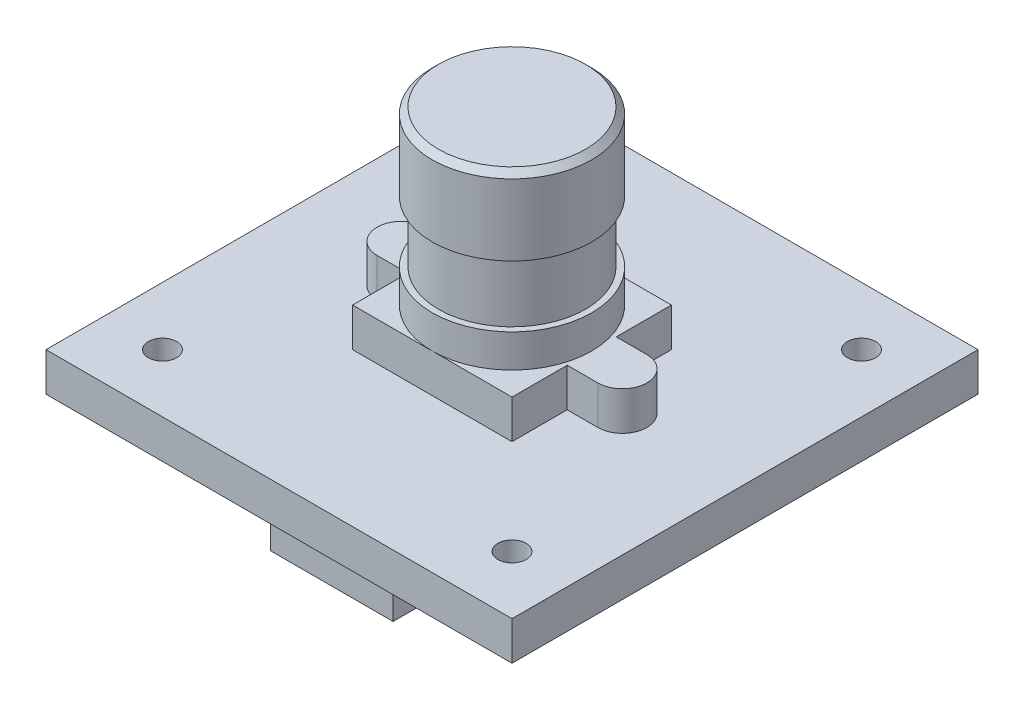
SolidWorks part; units mm, degrees
ref_plane "前视基准面" through (0, 0, 0) normal (0, 0, 1) x (1, 0, 0)
ref_plane "上视基准面" through (0, 0, 0) normal (0, 1, 0) x (1, 0, 0)
ref_plane "右视基准面" through (0, 0, 0) normal (1, 0, 0) x (0, 0, -1)
sketch "草图2" plane through (0, 0, 0) normal (0, 1, 0) x (1, 0, 0)
  line L0 (0, -55) -> (0, 55) construction
  line L1 (-19, 19) -> (19, 19)
  line L2 (-19, 19) -> (-19, -19)
  line L3 (-19, -19) -> (19, -19)
  line L4 (19, 19) -> (19, -19)
  line L5 (-55, 0) -> (55, 0) construction
  circle A0 centre (14.25, 14.25) radius 1.15
  circle A1 centre (-14.25, 14.25) radius 1.15
  circle A2 centre (14.25, -14.25) radius 1.15
  circle A3 centre (-14.25, -14.25) radius 1.15
  dimension "D5" = 2.3
  dimension "D1" = 38
  dimension "D2" = 38
  dimension "D3" = 19
  dimension "D4" = 19
  dimension "D6" = 4.75
  dimension "D7" = 4.75
extrude "凸台-拉伸1" add sketch "草图2" along normal blind 3.15
sketch "草图3" plane through (0, 0, 0) normal (0, 1, 0) x (1, 0, 0)
  line L0 (9, 2) -> (6.5, 2)
  line L1 (-6.5, 6.5) -> (6.5, 6.5)
  line L2 (-6.5, 6.5) -> (-6.5, -6.5)
  line L3 (-6.5, -6.5) -> (6.5, -6.5)
  line L4 (6.5, 6.5) -> (6.5, -6.5)
  line L5 (9, -2) -> (6.5, -2)
  line L6 (0, -1.65) -> (0, 1.65) construction
  line L7 (-9, -2) -> (-6.5, -2)
  line L8 (-9, 2) -> (-6.5, 2)
  arc A0 (9, -2) -> (9, 2) centre (9, 0) ccw
  arc A1 (-9, -2) -> (-9, 2) centre (-9, 0) cw
  dimension "D5" = 4
  dimension "D1" = 13
  dimension "D2" = 13
  dimension "D3" = 6.5
  dimension "D4" = 6.5
  dimension "D6" = 2.5
extrude "凸台-拉伸2" add sketch "草图3" along normal blind 3.15 from surface at 3.15 contours A1 L7 L2 L8 | L4 L1 L2 L3 | L5 A0 L0 L4 starting at face at (14.25, 3.15, 13.1)
sketch "草图4" plane through (0, 0, 0) normal (0, 1, 0) x (1, 0, 0)
  circle A0 centre (0, 0) radius 6.5
  dimension "D1" = 13
extrude "凸台-拉伸3" add sketch "草图4" along normal blind 14 from surface at 6.3 starting at face at (0, 6.3, 0)
sketch "草图5" plane through (0, 0, 0) normal (0, 1, 0) x (1, 0, 0)
  circle A0 centre (0, 0) radius 6
  circle A2 centre (0, 0) radius 32.561
  dimension "D1" = 12
extrude "切除-拉伸1" cut sketch "草图5" along normal blind 5 from offset 9
sketch "草图6" plane through (0, 0, 0) normal (0, 1, 0) x (1, 0, 0)
  line L0 (-19, -19) -> (19, -19) construction
  line L1 (-5, -10) -> (5, -10)
  line L2 (-5, -10) -> (-5, -14.7)
  line L3 (-5, -14.7) -> (5, -14.7)
  line L4 (5, -10) -> (5, -14.7)
  dimension "D1" = 10
  dimension "D2" = 4.7
  dimension "D3" = 5
  dimension "D4" = 9
extrude "凸台-拉伸4" add sketch "草图6" against normal blind 6.2
chamfer "倒角1" distance 0.5 angle 45 1 edges at (0, 20.3, 6.5)
equation "\"4。75\"=4.71051"
